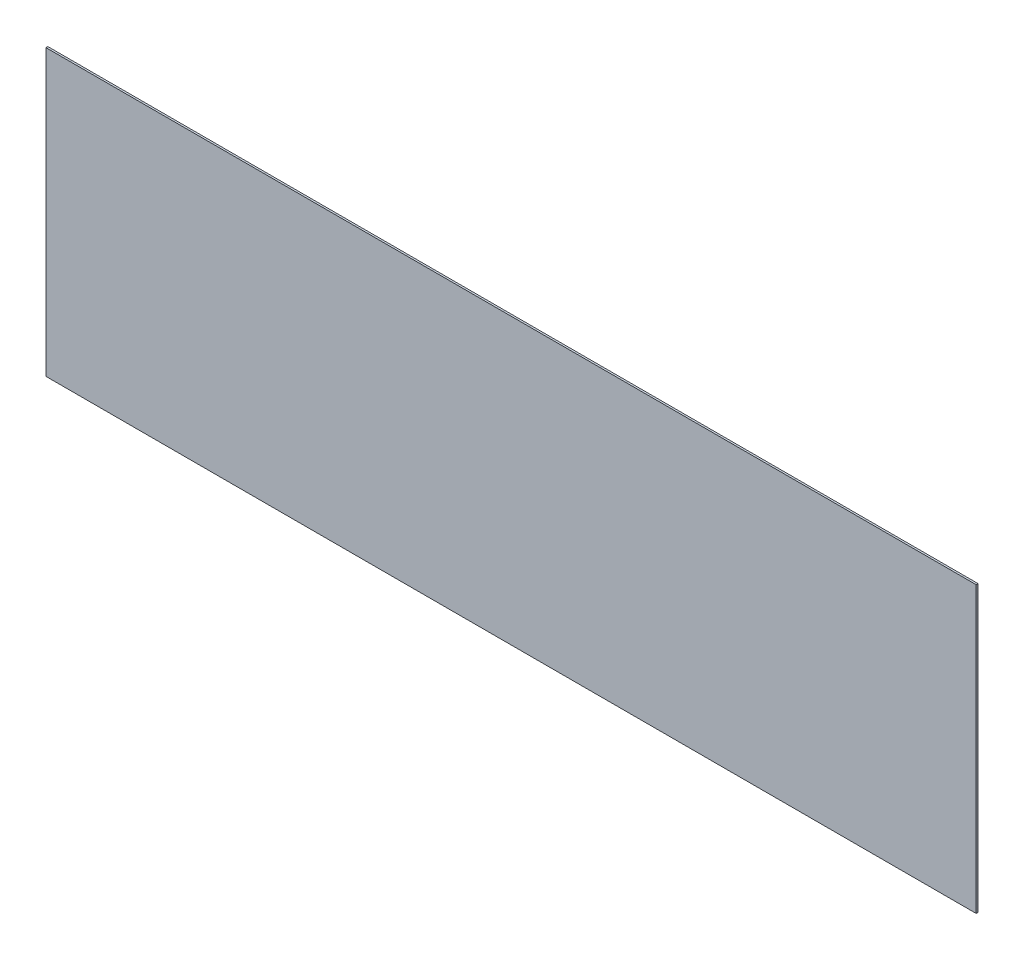
SolidWorks part; units mm, degrees
material "paste"
ref_plane "Ön Düzlem" through (0, 0, 0) normal (0, 0, 1) x (1, 0, 0)
ref_plane "Üst Düzlem" through (0, 0, 0) normal (0, 1, 0) x (1, 0, 0)
ref_plane "Sağ Düzlem" through (0, 0, 0) normal (1, 0, 0) x (0, 0, -1)
sketch "Sketch1" plane through (0, 0, 0) normal (0, 0, 1) x (1, 0, 0)
  line L1 (-22.8798, 11.1962) -> (26.1202, 11.1962)
  line L2 (-22.8798, 11.1962) -> (-22.8798, -3.8038)
  line L3 (-22.8798, -3.8038) -> (26.1202, -3.8038)
  line L4 (26.1202, 11.1962) -> (26.1202, -3.8038)
  dimension "D1" = 49
  dimension "D2" = 15
extrude "Boss-Extrude1" add sketch "Sketch1" along normal blind 0.1
